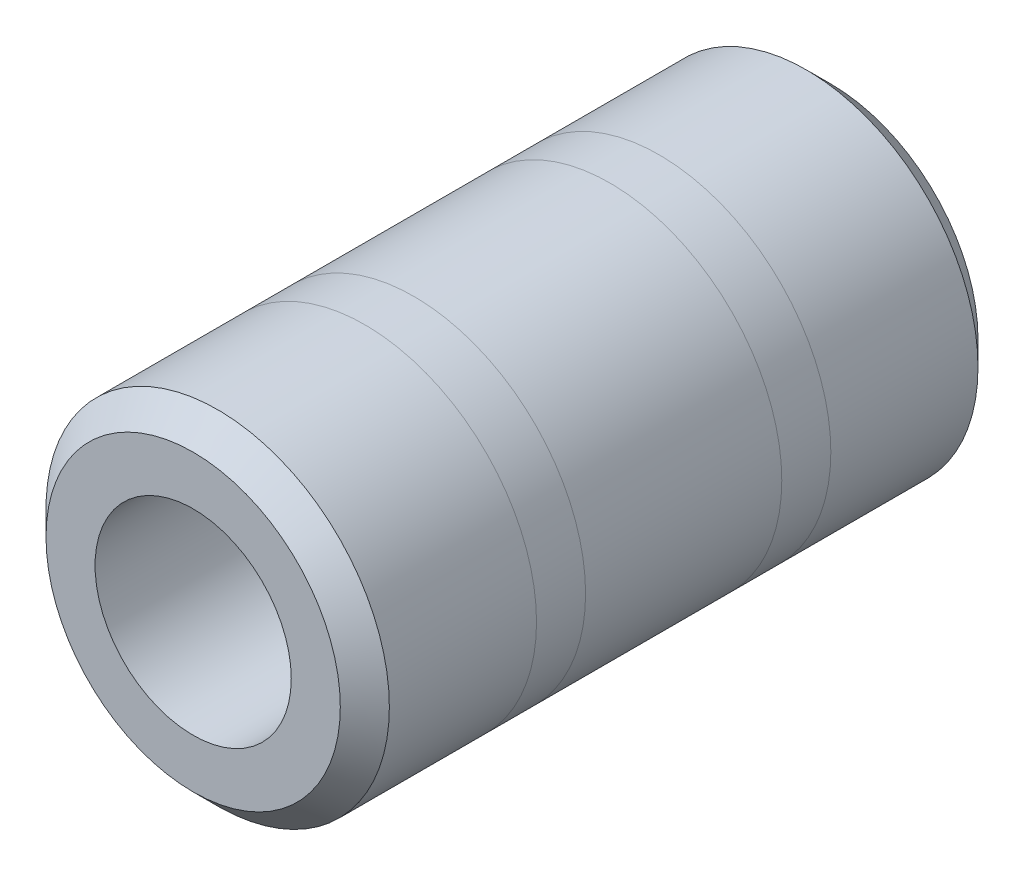
SolidWorks part; units mm, degrees
material "AISI 4340 Steel, normalized"
ref_plane "Front Plane" through (0, 0, 0) normal (0, 0, 1) x (1, 0, 0)
ref_plane "Top Plane" through (0, 0, 0) normal (0, 1, 0) x (1, 0, 0)
ref_plane "Right Plane" through (0, 0, 0) normal (1, 0, 0) x (0, 0, -1)
sketch "Sketch1" plane through (0, 0, 0) normal (0, 0, 1) x (1, 0, 0)
  circle A0 centre (0, 0) radius 17.5
  dimension "D1" = 35
extrude "Boss-Extrude1" add sketch "Sketch1" along normal blind 65
sketch "Sketch2" plane through (0, 0, 65) normal (0, 0, 1) x (1, 0, 0)
  circle A0 centre (0, 0) radius 10
  dimension "D1" = 20
extrude "Cut-Extrude1" cut sketch "Sketch2" against normal through all both and the other way through all
chamfer "Chamfer1" distance 2.5 angle 45 2 edges at (17.5, 0, 65) (17.5, 0, 0)
ref_plane "Plane1" through (0, 0, 42.5) normal (0, 0, 1) x (1, 0, 0)
ref_plane "Plane2" through (0, 0, 22.5) normal (0, 0, 1) x (1, 0, 0)
ref_plane "Plane3" through (0, 0, 17.5) normal (0, 0, 1) x (1, 0, 0)
ref_plane "Plane4" through (0, 0, 2.5) normal (0, 0, 1) x (1, 0, 0)
ref_plane "Plane5" through (0, 0, 47.5) normal (0, 0, 1) x (1, 0, 0)
ref_plane "Plane6" through (0, 0, 62.5) normal (0, 0, 1) x (1, 0, 0)
split line "Split Line2"
split line "Split Line3"
split line "Split Line4"
split line "Split Line5"
